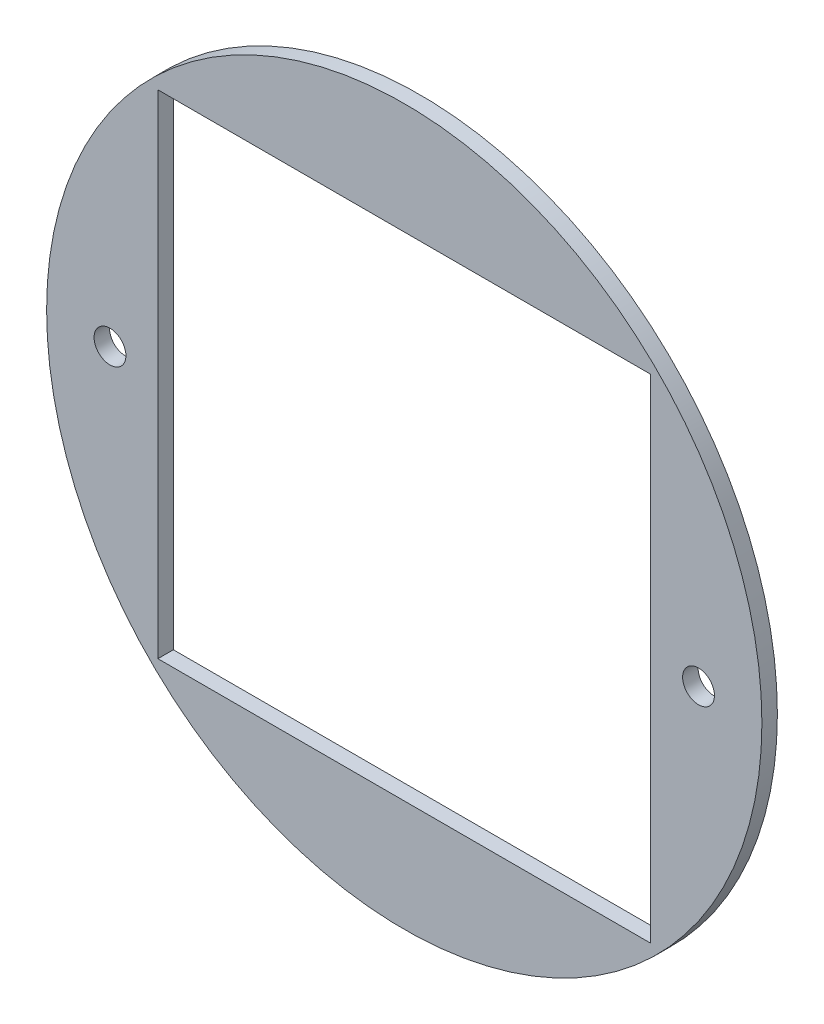
SolidWorks part; units mm, degrees
material "6061 Alloy"
ref_plane "Front Plane" through (0, 0, 0) normal (0, 0, 1) x (1, 0, 0)
ref_plane "Top Plane" through (0, 0, 0) normal (0, 1, 0) x (1, 0, 0)
ref_plane "Right Plane" through (0, 0, 0) normal (1, 0, 0) x (0, 0, -1)
sketch "Sketch1" plane through (0, 0, 0) normal (0, 0, 1) x (1, 0, 0)
  circle A0 centre (0, 0) radius 73.3171
  dimension "D1" = 146.6342
extrude "Boss-Extrude1" add sketch "Sketch1" along normal blind 3.175
sketch "Sketch2" plane through (0, 0, 3.175) normal (0, 0, 1) x (1, 0, 0)
  point P0 (-60.325, 0)
  point P1 (60.325, 0)
  dimension "D1" = 60.325
  dimension "D2" = 60.325
hole_wizard "1/4 Clearance Hole1" positions "Sketch2" profile "Sketch3" hole size "1/4" standard "ANSI Inch" end condition through all
sketch "Sketch3" plane through (-60.325, 0, 3.175) normal (1, 0, 0) x (0, -1, 0)
  line L0 (0, 0) -> (0, 3.175)
  line L1 (0, 3.175) -> (3.2639, 3.175)
  line L2 (3.2639, 3.175) -> (3.2639, 0)
  line L5 (3.2639, 0) -> (0, 0)
  line L11 (0, -6.35) -> (0, 107.95) construction
  dimension "Thru Hole Dia." = 6.5278
  dimension "Thru Hole Depth" = 3.175
sketch "Sketch4" plane through (0, 0, 3.175) normal (0, 0, 1) x (1, 0, 0)
  line L1 (-50.5, -50.5) -> (50.5, -50.5)
  line L2 (-50.5, -50.5) -> (-50.5, 50.5)
  line L3 (-50.5, 50.5) -> (50.5, 50.5)
  line L4 (50.5, -50.5) -> (50.5, 50.5)
  line L5 (-50.5, -50.5) -> (50.5, 50.5) construction
  line L6 (-50.5, 50.5) -> (50.5, -50.5) construction
  point P0 (0, 0)
  dimension "D1" = 101
  dimension "D2" = 101
extrude "Cut-Extrude1" cut sketch "Sketch4" against normal through all both and the other way through all
equation "\"outerdiameter\"= 5.773"
equation "\"platethickness\"= 1 / 8"
equation "\"holespacing\"= 2.375"
equation "\"D1@Sketch1\"=\"outerdiameter\""
equation "\"D1@Boss-Extrude1\"=\"platethickness\""
equation "\"D1@Sketch2\"=\"holespacing\""
equation "\"D2@Sketch2\"=\"holespacing\""
equation "\"cutclearance\"= 101mm"
equation "\"D1@Sketch4\"=\"cutclearance\""
equation "\"D2@Sketch4\"=\"cutclearance\""
